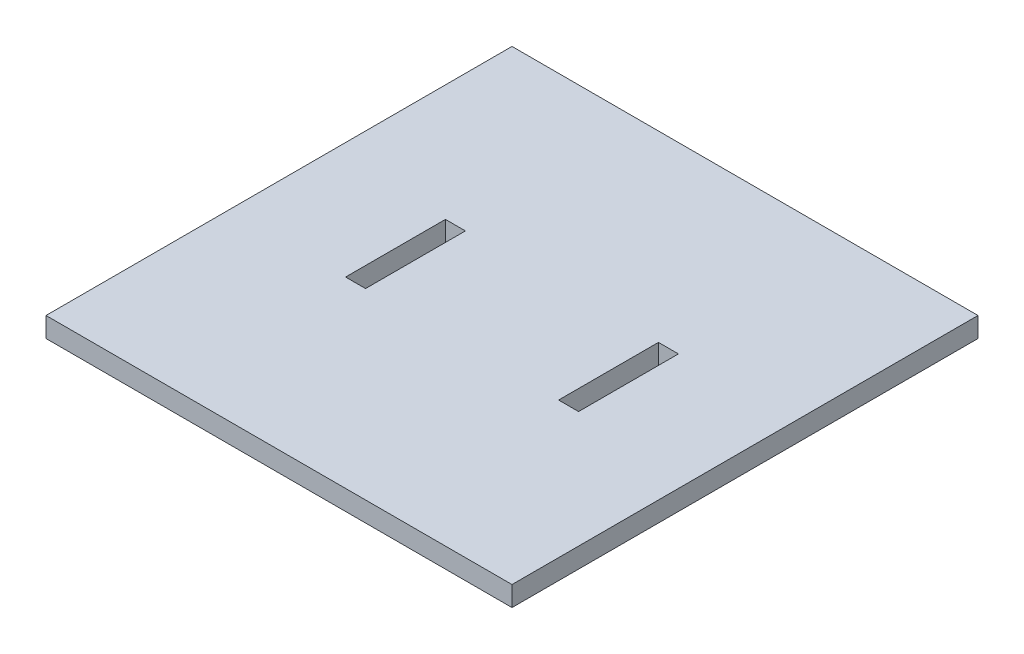
SolidWorks part; units mm, degrees
ref_plane "Plano frontal" through (0, 0, 0) normal (0, 0, 1) x (1, 0, 0)
ref_plane "Plano superior" through (0, 0, 0) normal (0, 1, 0) x (1, 0, 0)
ref_plane "Plano direito" through (0, 0, 0) normal (1, 0, 0) x (0, 0, -1)
sketch "Esboço1" plane through (0, 0, 0) normal (0, 1, 0) x (1, 0, 0)
  line L1 (-14.1495, 27.3582) -> (55.8505, 27.3582)
  line L2 (-14.1495, 27.3582) -> (-14.1495, -42.6418)
  line L3 (-14.1495, -42.6418) -> (55.8505, -42.6418)
  line L4 (55.8505, 27.3582) -> (55.8505, -42.6418)
  dimension "D1" = 70
  dimension "D2" = 70
extrude "Ressalto-extrusão1" add sketch "Esboço1" along normal blind 3
sketch "Esboço2" plane through (0, 3, 0) normal (0, 1, 0) x (1, 0, 0)
  line L0 (3.3505, -0.1418) -> (3.3505, -15.1418)
  line L1 (3.3505, -15.1418) -> (6.3505, -15.1418)
  line L2 (6.3505, -15.1418) -> (6.3505, -0.1418)
  line L3 (6.3505, -0.1418) -> (3.3505, -0.1418)
  line L4 (20.8505, 27.3582) -> (20.8505, -42.6418) construction
  line L5 (55.8505, 27.3582) -> (-14.1495, 27.3582) construction
  line L6 (-14.1495, -42.6418) -> (55.8505, -42.6418) construction
  line L7 (35.3505, -15.1418) -> (35.3505, -0.1418)
  line L8 (38.3505, -15.1418) -> (35.3505, -15.1418)
  line L9 (38.3505, -0.1418) -> (38.3505, -15.1418)
  line L10 (35.3505, -0.1418) -> (38.3505, -0.1418)
  point P10 (4.8505, -0.1418)
  dimension "D1" = 14.5
  dimension "D2" = 3
  dimension "D3" = 15
  dimension "D4" = 27.5
extrude "Corte-extrusão1" cut sketch "Esboço2" against normal up to surface (3 mm away) up to face at (20.8505, 0, 7.6418)
